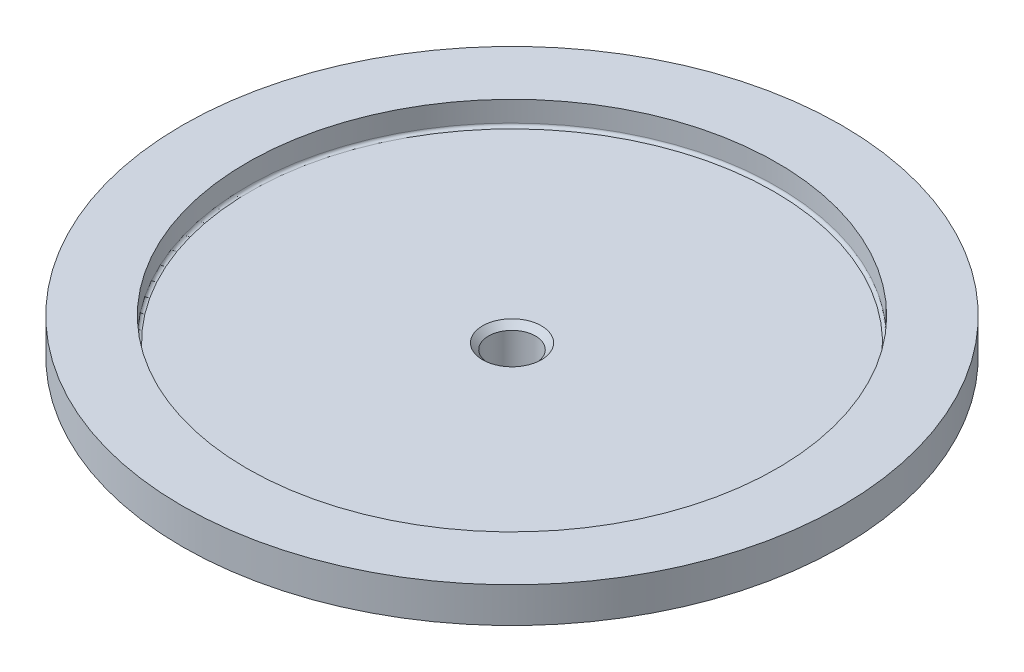
SolidWorks part; units mm, degrees
ref_plane "Front Plane" through (0, 0, 0) normal (0, 0, 1) x (1, 0, 0)
ref_plane "Top Plane" through (0, 0, 0) normal (0, 1, 0) x (1, 0, 0)
ref_plane "Right Plane" through (0, 0, 0) normal (1, 0, 0) x (0, 0, -1)
sketch "Sketch1" plane through (0, 0, 0) normal (0, 1, 0) x (1, 0, 0)
  circle A0 centre (0, 0) radius 56
extrude "Extrude1" add sketch "Sketch1" along normal blind 7.5
sketch "Sketch2" plane through (0, 0, 0) normal (0, -1, 0) x (1, 0, 0)
  circle A0 centre (0, 0) radius 10
extrude "Extrude5" add sketch "Sketch2" along normal blind 35
sketch "Sketch5" plane through (0, 7.5, 0) normal (0, 1, 0) x (1, 0, 0)
  circle A0 centre (0, 0) radius 45
extrude "Extrude6" cut sketch "Sketch5" against normal blind 4
sketch "Sketch6" plane through (0, 3.5, 0) normal (0, 1, 0) x (1, 0, 0)
  circle A0 centre (0, 0) radius 4
extrude "Extrude7" cut sketch "Sketch6" against normal through all
chamfer "Chamfer3" distance 1 angle 45 1 edges at (0, 3.5, 4)
ref_plane "Plane1" through (0, 0, 10) normal (0, 0, 1) x (1, 0, 0)
sketch "Sketch7" plane through (0, 0, 10) normal (0, 0, 1) x (1, 0, 0)
  line L0 (-10, 0) -> (-10, -23)
  line L1 (-10, 0) -> (-10, -35) construction
  line L2 (-10, -23) -> (-8.9393, -23)
  line L3 (-8.9393, -23) -> (-8.9393, -24.6893)
  line L4 (-8.9393, -24.6893) -> (-10, -25.75)
  line L5 (-10, -23) -> (-10, -25.75)
extrude "Extrude8" cut sketch "Sketch7" against normal through all contours L2 L3 L4 L5
mirror "Mirror2" about plane through (0, 0, 0) normal (1, 0, 0) of "Extrude8"
sketch "Sketch9" plane through (0, 0, 10) normal (0, 0, 1) x (1, 0, 0)
  line L0 (-10, -25.75) -> (-10, -32.25)
  line L1 (-10, -25.75) -> (-10, -35) construction
  line L2 (-10, -32.25) -> (-9.1161, -33.1339)
  line L3 (-9.1161, -33.1339) -> (-9.1161, -34.1339)
  line L4 (-9.1161, -34.1339) -> (-8.25, -35)
  line L5 (-10, -35) -> (10, -35) construction
  line L6 (-8.25, -35) -> (-10, -35)
  line L7 (-10, -35) -> (-10, -32.25)
extrude "Extrude10" cut sketch "Sketch9" against normal through all contours L7 L6 L4 L3 L2
mirror "Mirror3" about plane through (0, 0, 0) normal (1, 0, 0) of "Extrude10"
sketch "Sketch10" plane through (0, 0, 10) normal (0, 0, 1) x (1, 0, 0)
  line L1 (10, -23) -> (-10, -23)
  line L2 (10, -23) -> (10, -35.4831)
  line L3 (10, -35.4831) -> (-10, -35.4831)
  line L4 (-10, -23) -> (-10, -35.4831)
extrude "Extrude11" cut sketch "Sketch10" against normal through all
sketch "Sketch11" plane through (0, -23, 0) normal (0, -1, 0) x (1, 0, 0)
  circle A0 centre (0, 0) radius 7.5
extrude "Extrude12" add sketch "Sketch11" along normal blind 1.5
sketch "Sketch12" plane through (0, -24.5, 0) normal (0, -1, 0) x (1, 0, 0)
  circle A0 centre (0, 0) radius 10
extrude "Extrude13" add sketch "Sketch12" along normal blind 5
sketch "Sketch13" plane through (0, -29.5, 0) normal (0, -1, 0) x (1, 0, 0)
  circle A0 centre (0, 0) radius 7.5
extrude "Extrude15" add sketch "Sketch13" along normal blind 3
chamfer "Chamfer4" distance 1.5 angle 45 1 edges at (0, -32.5, -7.5)
chamfer "Chamfer6" distance 1.5 angle 45 1 edges at (0, -24.5, -10)
chamfer "Chamfer7" distance 1.5 angle 45 1 edges at (0, -29.5, -10)
sketch "Sketch16" plane through (0, -23, 0) normal (0, 1, 0) x (-1, 0, 0)
  circle A0 centre (0, 0) radius 4
  point P3 (7.1005, -4.5608)
extrude "Extrude16" cut sketch "Sketch16" against normal through all
sketch "Sketch17" plane through (0, 0, 0) normal (0, -1, 0) x (1, 0, 0)
  circle A0 centre (0, 0) radius 51
extrude "Extrude17" cut sketch "Sketch17" against normal blind 1.5 flip side to cut
fillet "Fillet7" radius 0.5 1 edges at (0, 3.5, 45)
